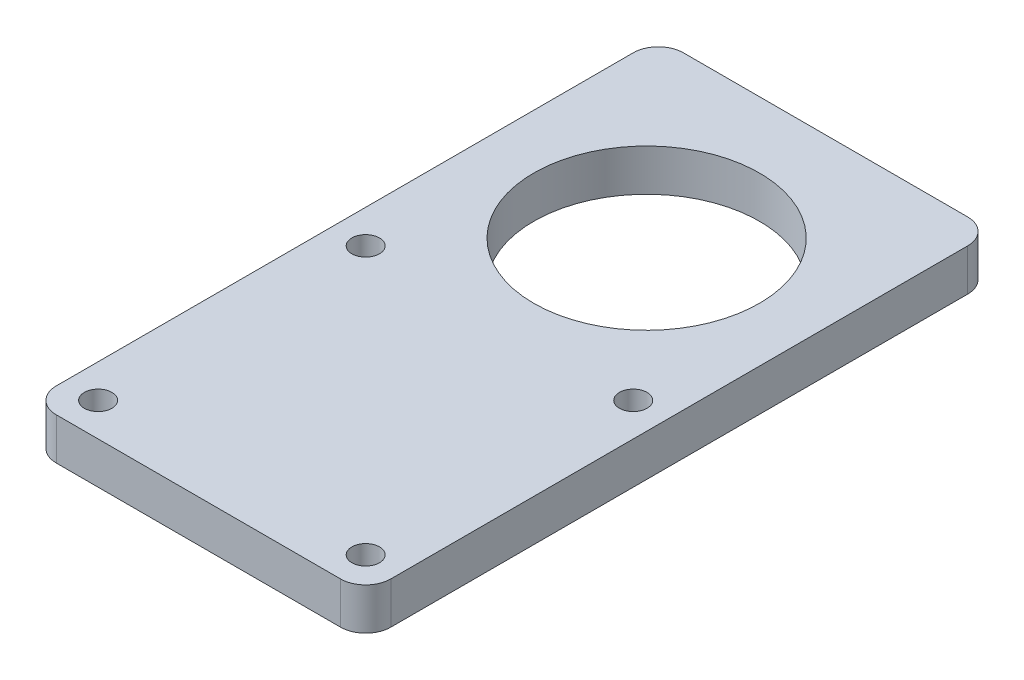
SolidWorks part; units mm, degrees
ref_plane "前视基准面" through (0, 0, 0) normal (0, 0, 1) x (1, 0, 0)
ref_plane "上视基准面" through (0, 0, 0) normal (0, 1, 0) x (1, 0, 0)
ref_plane "右视基准面" through (0, 0, 0) normal (1, 0, 0) x (0, 0, -1)
sketch "草图1" plane through (0, 0, 0) normal (0, 1, 0) x (1, 0, 0)
  line L0 (48.464, -47.4) -> (-15.2363, -47.4) construction
  line L1 (-20, -20) -> (20, -20)
  line L2 (-20, -20) -> (-20, 55)
  line L3 (-20, 55) -> (20, 55)
  line L4 (20, -20) -> (20, 55)
  line L5 (-20, -20) -> (20, 55) construction
  line L6 (-20, 55) -> (20, -20) construction
  line L7 (-16, -16) -> (16, -16) construction
  line L8 (-16, -16) -> (-16, 16) construction
  line L9 (-16, 16) -> (16, 16) construction
  line L10 (16, -16) -> (16, 16) construction
  line L11 (-16, -16) -> (16, 16) construction
  line L12 (-16, 16) -> (16, -16) construction
  line L13 (55.6003, 33.6) -> (-58.752, 33.6) construction
  circle A0 centre (-16, 16) radius 1.65
  circle A1 centre (16, 16) radius 1.65
  circle A2 centre (16, -16) radius 1.65
  circle A3 centre (-16, -16) radius 1.65
  circle A4 centre (0, 33.6) radius 13.5
  point P0 (0, 17.5)
  point P6 (0, 17.5)
  point P18 (0, 0)
  dimension "D3" = 3.3
  dimension "D8" = 27
  dimension "D1" = 40
  dimension "D2" = 75
  dimension "D4" = 32
  dimension "D5" = 4
  dimension "D6" = 27.4
  dimension "D7" = 81
extrude "凸台-拉伸1" add sketch "草图1" along normal blind 5
fillet "圆角1" radius 3 4 edges at (-20, 2.5, 20) (20, 2.5, -55) (-20, 2.5, -55) (20, 2.5, 20)
